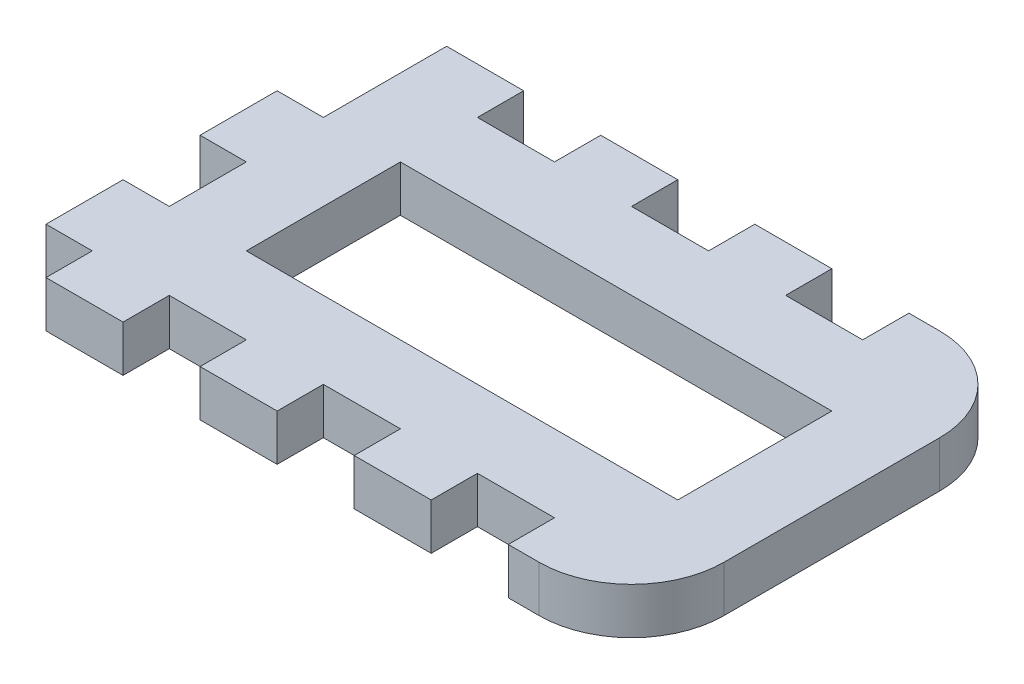
SolidWorks part; units mm, degrees
ref_plane "Front Plane" through (0, 0, 0) normal (0, 0, 1) x (1, 0, 0)
ref_plane "Top Plane" through (0, 0, 0) normal (0, 1, 0) x (1, 0, 0)
ref_plane "Right Plane" through (0, 0, 0) normal (1, 0, 0) x (0, 0, -1)
sketch "Sketch1" plane through (0, 0, 0) normal (0, 1, 0) x (1, 0, 0)
  line L1 (-19, 13) -> (19, 13)
  line L2 (-19, 13) -> (-19, -13)
  line L3 (-19, -13) -> (19, -13)
  line L4 (19, 13) -> (19, -13)
  line L5 (-19, 13) -> (19, -13) construction
  line L6 (-19, -13) -> (19, 13) construction
  point P0 (0, 0)
  dimension "D1" = 38
  dimension "D2" = 26
extrude "Boss-Extrude1" add sketch "Sketch1" along normal mid plane 3
sketch "Sketch8" plane through (-19, 0, 0) normal (-1, 0, 0) x (0, 0, 1)
  line L0 (-13, -1.5) -> (13, -1.5) construction
  line L1 (-13, 1.5) -> (-10, 1.5)
  line L2 (-13, 1.5) -> (-13, -1.5)
  line L3 (-13, -1.5) -> (-10, -1.5)
  line L4 (-10, 1.5) -> (-10, -1.5)
  line L6 (13, 1.5) -> (10, 1.5)
  line L7 (13, 1.5) -> (13, -1.5)
  line L8 (13, -1.5) -> (10, -1.5)
  line L9 (10, 1.5) -> (10, -1.5)
  line L10 (-10, 1.5) -> (-5, 1.5)
  line L11 (-10, 1.5) -> (-10, -1.5)
  line L12 (-10, -1.5) -> (-5, -1.5)
  line L13 (-5, 1.5) -> (-5, -1.5)
  line L18 (5, 1.5) -> (10, 1.5)
  line L19 (5, 1.5) -> (5, -1.5)
  line L20 (5, -1.5) -> (10, -1.5)
  line L21 (10, 1.5) -> (10, -1.5)
  line L22 (-5, 1.5) -> (0, 1.5)
  line L23 (-5, 1.5) -> (-5, -1.5)
  line L24 (-5, -1.5) -> (0, -1.5)
  line L25 (0, 1.5) -> (0, -1.5)
  line L26 (5, 1.5) -> (0, 1.5)
  line L27 (5, 1.5) -> (5, -1.5)
  line L28 (5, -1.5) -> (0, -1.5)
  line L29 (0, 1.5) -> (0, -1.5)
  line M12 (-13, -1.5) -> (13, -1.5)
  line M14 (13, 1.5) -> (-13, 1.5)
  dimension "D1" = 3
extrude "Boss-Extrude2" add sketch "Sketch8" along normal blind 3 contours L25 L13 M14 M12 | L19 L9 M14 M12 | L22
sketch "Sketch9" plane through (0, -1.5, 0) normal (0, -1, 0) x (1, 0, 0)
  line L0 (-19, 13) -> (19, 13) construction
  line L1 (-14, 13) -> (-19, 13)
  line L2 (-14, 13) -> (-14, 10)
  line L3 (-14, 10) -> (-19, 10)
  line L4 (-19, 13) -> (-19, 10)
  line L5 (-22, 10) -> (-19, 10) construction
  line L6 (-14, 10) -> (-9, 10)
  line L7 (-14, 10) -> (-14, 13)
  line L8 (-14, 13) -> (-9, 13)
  line L9 (-9, 10) -> (-9, 13)
  line L10 (0, 0) -> (-6.2512, 0) construction
  line L11 (-14, -13) -> (-9, -13)
  line L12 (-9, -10) -> (-9, -13)
  line L13 (-14, -10) -> (-9, -10)
  line L14 (-14, -10) -> (-14, -13)
  line L15 (-14, -10) -> (-19, -10)
  line L16 (-19, -13) -> (-19, -10)
  line L17 (-14, -13) -> (-19, -13)
  line L18 (-14, -13) -> (-14, -10)
  line L19 (-4, -10) -> (1, -10)
  line L20 (-9, 13) -> (-4, 13)
  line L21 (-9, 13) -> (-9, 10)
  line L22 (-9, 10) -> (-4, 10)
  line L23 (-4, 13) -> (-4, 10)
  line L24 (-4, 13) -> (1, 13)
  line L25 (-4, 13) -> (-4, 10)
  line L26 (-4, 10) -> (1, 10)
  line L27 (1, 13) -> (1, 10)
  line L28 (1, -13) -> (1, -10)
  line L29 (-4, -13) -> (1, -13)
  line L30 (-4, -13) -> (-4, -10)
  line L31 (-9, -10) -> (-4, -10)
  line L32 (-4, -13) -> (-4, -10)
  line L33 (-9, -13) -> (-4, -13)
  line L34 (-9, -13) -> (-9, -10)
  line L35 (1, -13) -> (6, -13)
  line L36 (1, 10) -> (6, 10)
  line L37 (1, 10) -> (1, 13)
  line L38 (1, 13) -> (6, 13)
  line L39 (6, 10) -> (6, 13)
  line L40 (6, 10) -> (11, 10)
  line L41 (6, 10) -> (6, 13)
  line L42 (6, 13) -> (11, 13)
  line L43 (11, 10) -> (11, 13)
  line L44 (11, 10) -> (16, 10)
  line L45 (11, 10) -> (11, 13)
  line L46 (11, 13) -> (16, 13)
  line L47 (16, 10) -> (16, 13)
  line L48 (6, -10) -> (6, -13)
  line L49 (1, -10) -> (6, -10)
  line L50 (1, -10) -> (1, -13)
  line L51 (6, -13) -> (11, -13)
  line L52 (11, -10) -> (11, -13)
  line L53 (6, -10) -> (11, -10)
  line L54 (6, -10) -> (6, -13)
  line L55 (11, -13) -> (16, -13)
  line L56 (16, -10) -> (16, -13)
  line L57 (11, -10) -> (16, -10)
  line L58 (11, -10) -> (11, -13)
  line M15 (19, 13) -> (-19, 13)
  line M25 (-19, -13) -> (19, -13)
  dimension "D1" = 5
extrude "Cut-Extrude2" cut sketch "Sketch9" against normal up to surface (3 mm away) contours L13 L14 L12 M25 | L6 L9 L2 M15 | L30 L28 L19 M25 | L27 L23 L26 M15 | L53 L48 L52 M25 | L40 L43 L39 M15
fillet "Fillet1" radius 6 2 edges at (19, 0, 13) (19, 0, -13)
sketch "Sketch10" plane through (0, 1.5, 0) normal (0, 1, 0) x (1, 0, 0)
  line L0 (-19, 13) -> (-19, 5) construction
  line L1 (14, 5) -> (-14, 5)
  line L2 (14, 5) -> (14, -5)
  line L3 (14, -5) -> (-14, -5)
  line L4 (-14, 5) -> (-14, -5)
  line L5 (14, 5) -> (-14, -5) construction
  line L6 (14, -5) -> (-14, 5) construction
  point P0 (0, 0)
  dimension "D1" = 10
  dimension "D2" = 5
extrude "Cut-Extrude3" cut sketch "Sketch10" against normal up to surface (3 mm away)
